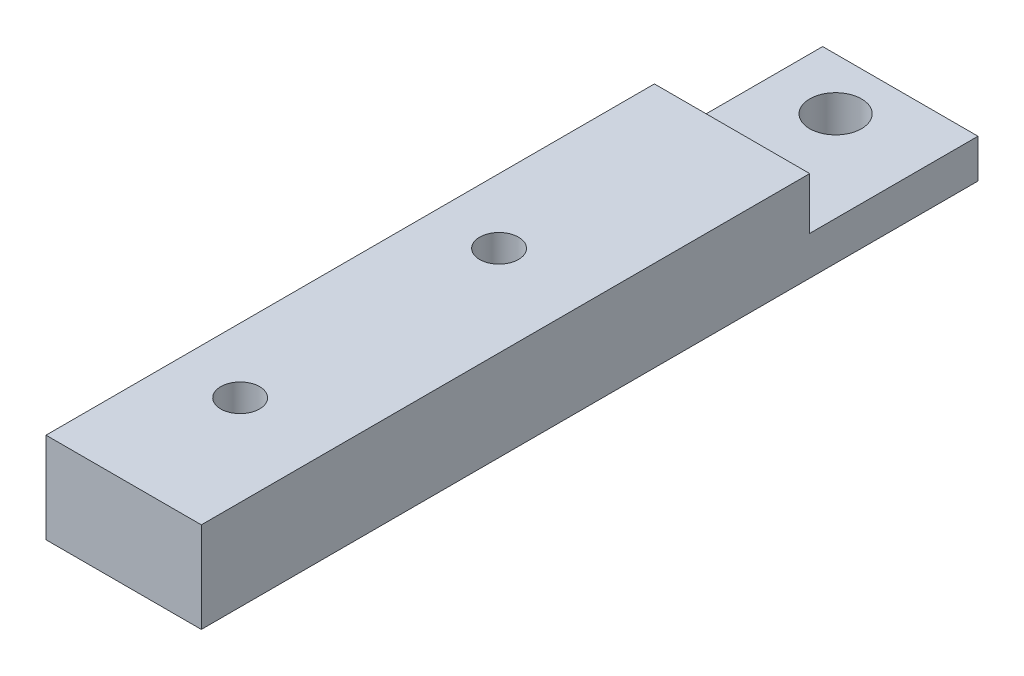
SolidWorks part; units mm, degrees
ref_plane "Front" through (0, 0, 0) normal (0, 0, 1) x (1, 0, 0)
ref_plane "Top" through (0, 0, 0) normal (0, 1, 0) x (1, 0, 0)
ref_plane "Right" through (0, 0, 0) normal (1, 0, 0) x (0, 0, -1)
sketch "Sketch1" plane through (0, 0, 0) normal (0, 1, 0) x (1, 0, 0)
  line L1 (-5, 30) -> (5, 30)
  line L2 (-5, 30) -> (-5, -30)
  line L3 (-5, -30) -> (5, -30)
  line L4 (5, 30) -> (5, -30)
  line L5 (-5, 30) -> (5, -30) construction
  line L6 (-5, -30) -> (5, 30) construction
  point P0 (0, 0)
  dimension "D1" = 10
  dimension "D2" = 60
extrude "Boss-Extrude1" add sketch "Sketch1" along normal blind 7
sketch "Sketch2" plane through (0, 7, 0) normal (0, 1, 0) x (1, 0, 0)
  line L0 (0, 49.4155) -> (0, -52.5786) construction
  line L1 (0, -50) -> (0, 50) construction
  line L3 (-5, 17) -> (5, 17)
  line L4 (-5, 17) -> (-5, 30)
  line L5 (-5, 30) -> (5, 30)
  line L6 (5, 17) -> (5, 30)
  line L7 (-5, 17) -> (5, 30) construction
  line L8 (-5, 30) -> (5, 17) construction
  point P5 (0, 23.5)
  dimension "D1" = 13
extrude "Cut-Extrude1" cut sketch "Sketch2" against normal blind 4
sketch "Sketch3" plane through (0, 3, 0) normal (0, 1, 0) x (1, 0, 0)
  line L0 (0, -50) -> (0, 50) construction
  line L1 (5, 30) -> (-5, 30) construction
  circle A0 centre (0, 26) radius 2
  dimension "D2" = 4
  dimension "D1" = 4
extrude "Cut-Extrude2" cut sketch "Sketch3" against normal blind 4
sketch "Sketch4" plane through (0, 0, 0) normal (0, 1, 0) x (1, 0, 0)
  line L0 (0, -50) -> (0, 50) construction
  line L1 (-5, -30) -> (5, -30) construction
  circle A0 centre (0, 0) radius 1.5
  circle A1 centre (0, -20) radius 1.5
  dimension "D3" = 3
  dimension "D4" = 3
  dimension "D1" = 10
  dimension "D2" = 30
extrude "Cut-Extrude3" cut sketch "Sketch4" along normal blind 14
sketch "Sketch5" plane through (5, 0, 0) normal (1, 0, 0) x (0, 0, -1)
  line L0 (-30, 7) -> (-30, 0)
  line L1 (50, 0) -> (-50, 0) construction
  line L2 (-30, 7) -> (-30, 0) construction
  line L3 (-30, 0) -> (30, 0)
  line L4 (30, 3) -> (30, 0) construction
  line L5 (30, 0) -> (30, 3)
  line L6 (30, 3) -> (17, 3)
  line L7 (17, 3) -> (17, 7)
  line L8 (-30, 7) -> (17, 7) construction
  line L9 (17, 3) -> (17, 7) construction
  line L10 (17, 7) -> (-30, 7)
extrude "Boss-Extrude2" add sketch "Sketch5" along normal blind 2
